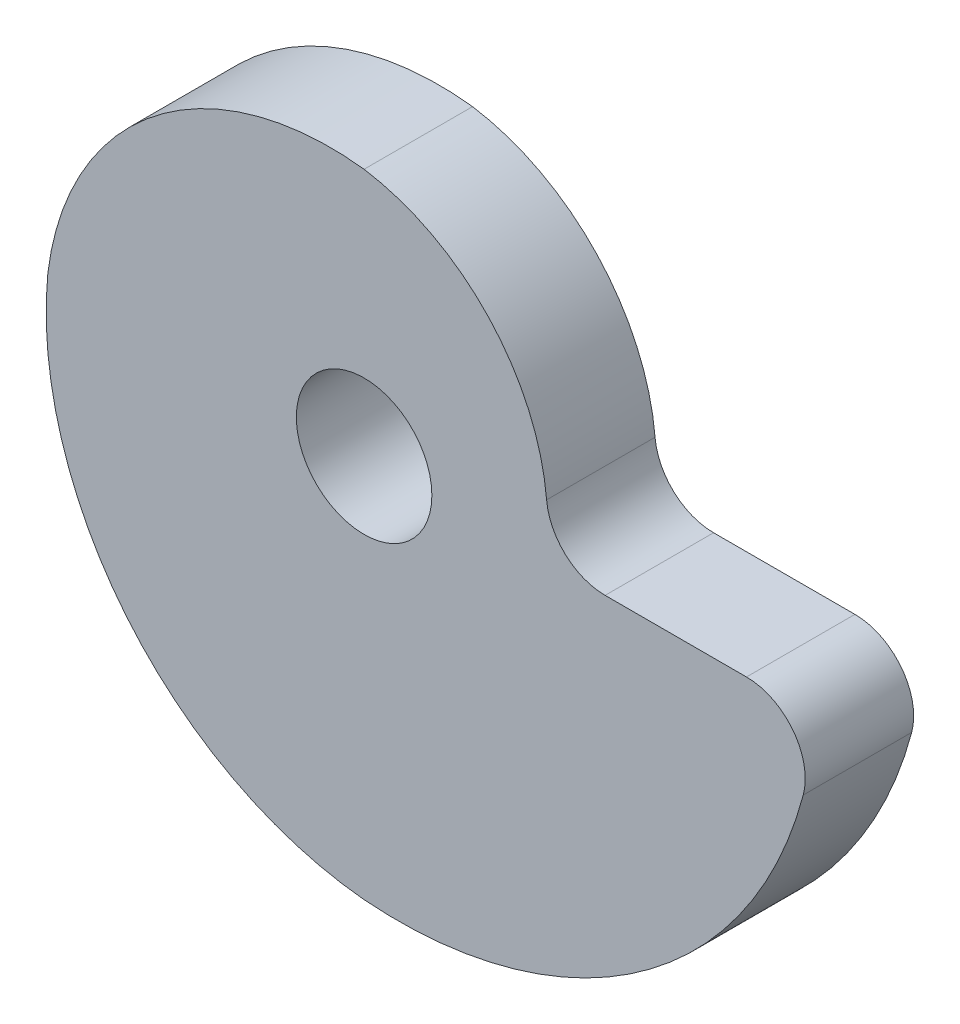
SolidWorks part; units mm, degrees
ref_plane "Front Plane" through (0, 0, 0) normal (0, 0, 1) x (1, 0, 0)
ref_plane "Top Plane" through (0, 0, 0) normal (0, 1, 0) x (1, 0, 0)
ref_plane "Right Plane" through (0, 0, 0) normal (1, 0, 0) x (0, 0, -1)
sketch "Sketch1" plane through (0, 0, 0) normal (0, 0, 1) x (1, 0, 0)
  line L0 (8, 0) -> (20, 0)
  circle A0 centre (0, 0) radius 3
  arc A6 (8, 0) -> (0, 11) centre (-1.5, 1.5) ccw
  arc A7 (0, 11) -> (-14, 0) centre (-1.5, -1.5) ccw
  arc A8 (-14, 0) -> (0, -17) centre (1.5, -1.5) ccw
  arc A9 (0, -17) -> (20, 0) centre (1.5, 1.5) ccw
  point P3 (-14, 0)
  point P4 (0, -17)
  point P7 (0, 11)
  point P14 (-13.8655, 1.9357)
  point P16 (1.8694, 10.84)
  point P17 (-1.2797, -16.9518)
  dimension "D1" = 0
  dimension "D2" = 11
  dimension "D3" = 6
  dimension "D4" = 14
  dimension "D5" = 8
  dimension "D6" = 17
  dimension "D9" = 18.5607
  dimension "D10" = 9.6177
  dimension "D11" = 12.5897
  dimension "D12" = 15.5724
  dimension "D7" = 0
  dimension "D8" = 0
  dimension "D13" = 12
extrude "Boss-Extrude1" add sketch "Sketch1" along normal mid plane 4.8
fillet "Fillet1" radius 2.6 2 edges at (20, 0, 0) (8, 0, 0)
sketch "Sketch3" plane through (0, 0, 0) normal (0, 0, 1) x (1, 0, 0)
  line L1 (15.091, 6.2633) -> (6.8553, 6.2633)
  line L2 (16.9251, 0) -> (10.6681, 0)
  line L4 (19.5251, -2.6) -> (31.9249, -2.6) construction
  line L5 (17.9623, 6.2633) -> (19.5251, -2.6) construction
  arc A3 (19.4379, -3.2679) -> (16.9251, 0) centre (16.9251, -2.6) ccw construction
  arc A4 (8.0786, 2.3659) -> (0, 11) centre (-1.5, 1.5) ccw construction
  arc A5 (15.091, 6.2633) -> (18.9756, 3.2172) centre (15.091, 2.2633) cw
  arc A7 (8.0786, 2.3659) -> (0, 11) centre (-1.5, 1.5) ccw
  arc A8 (6.8553, 6.2633) -> (0, 11) centre (-1.5, 1.5) ccw
  arc A9 (19.4379, -3.2679) -> (16.9251, 0) centre (16.9251, -2.6) ccw
  arc A10 (0, 11) -> (-14, 0) centre (-1.5, -1.5) ccw
  arc A11 (0, 11) -> (-14, 0) centre (-1.5, -1.5) ccw
  arc A12 (0, -17) -> (19.4379, -3.2679) centre (1.5, 1.5) ccw
  arc A13 (19.4379, -3.2679) -> (16.9251, 0) centre (16.9251, -2.6) ccw
  arc A14 (8.0786, 2.3659) -> (10.6681, 0) centre (10.6681, 2.6) ccw
  arc A15 (8.0786, 2.3659) -> (0, 11) centre (-1.5, 1.5) ccw
  arc A16 (0, 11) -> (-14, 0) centre (-1.5, -1.5) ccw
  arc A17 (-14, 0) -> (0, -17) centre (1.5, -1.5) ccw
  arc A18 (0, -17) -> (19.4379, -3.2679) centre (1.5, 1.5) ccw
  arc A23 (-14, 0) -> (0, -17) centre (1.5, -1.5) ccw
  arc A24 (19.4379, -3.2679) -> (19.5251, -2.6) centre (16.9251, -2.6) ccw
  arc A25 (19.5251, -2.6) -> (18.9756, 3.2172) centre (-0.4474, -1.5523) ccw
  point P13 (17.9623, 6.2633)
  dimension "D2" = 0
  dimension "D7" = 100
  dimension "D6" = 40
  dimension "D8" = 4
  dimension "D4" = 9
  dimension "D1" = 0
  dimension "D3" = 0
  dimension "D5" = 0
